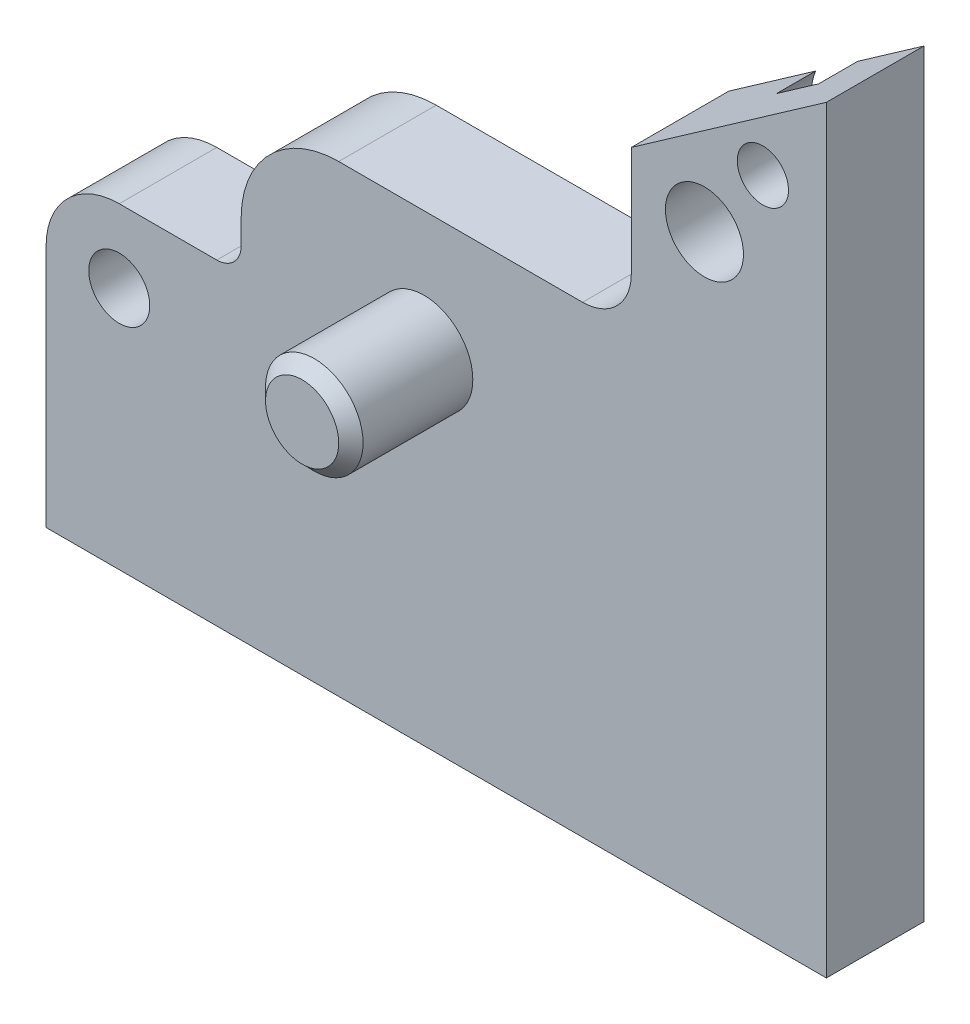
SolidWorks part; units mm, degrees
ref_plane "Front Plane" through (0, 0, 0) normal (0, 0, 1) x (1, 0, 0)
ref_plane "Top Plane" through (0, 0, 0) normal (0, 1, 0) x (1, 0, 0)
ref_plane "Right Plane" through (0, 0, 0) normal (1, 0, 0) x (0, 0, -1)
ref_plane "Plane1" through (0, 0, 4) normal (0, 0, 1) x (1, 0, 0)
sketch "Sketch1" plane through (0, 0, 4) normal (0, 0, 1) x (1, 0, 0)
  line L0 (32, 25.5) -> (0, 25.5)
  line L1 (0, 25.5) -> (0, 0)
  line L2 (0, 0) -> (32, 0)
  line L3 (32, 0) -> (32, 25.5)
extrude "Boss-Extrude1" add sketch "Sketch1" against normal blind 4
sketch "Sketch2" plane through (0, 0, 0) normal (0, 0, -1) x (-1, 0, 0)
  line L0 (-8, 25.5) -> (-8, 13)
  line L1 (-8, 13) -> (0, 13)
  line L2 (0, 13) -> (0, 25.5)
  line L3 (0, 25.5) -> (-8, 25.5)
extrude "Cut-Extrude1" cut sketch "Sketch2" against normal through all
sketch "Sketch3" plane through (0, 0, 0) normal (0, 0, -1) x (-1, 0, 0)
  line L0 (-24, 25.5) -> (-24, 19)
  line L1 (-24, 19) -> (-8, 19)
  line L2 (-8, 19) -> (-8, 25.5)
  line L3 (-8, 25.5) -> (-24, 25.5)
extrude "Cut-Extrude2" cut sketch "Sketch3" against normal through all
draft "Draft1" type of draft neutral plane draft angle 35 faces to draft 1 face at (28, 25.5, 2) neutral plane through (24, 25.5, 4) neutral plane normal (-1, 0, 0) parameters "D1"=35
ref_plane "Plane2" through (0, 5, 0) normal (0, 1, 0) x (1, 0, 0)
sketch "Sketch4" plane through (0, 5, 0) normal (0, 1, 0) x (1, 0, 0)
  line L0 (8, 5) -> (6, 5)
  line L1 (6, 5) -> (6, 0)
  line L2 (6, 0) -> (8, 0)
  line L3 (8, 0) -> (8, 5)
  line L4 (6, 5) -> (6, 0) construction
revolve "Revolve1" add sketch "Sketch4" angle 360 about L4
ref_plane "Plane3" through (0, 14, 0) normal (0, -1, 0) x (1, 0, 0)
sketch "Sketch5" plane through (0, 14, 0) normal (0, -1, 0) x (1, 0, 0)
  line L0 (17.5, 9) -> (15.5, 9)
  line L1 (15.5, 9) -> (15.5, 4)
  line L2 (15.5, 4) -> (17.5, 4)
  line L3 (17.5, 4) -> (17.5, 9)
  line L4 (15.5, 9) -> (15.5, 4) construction
revolve "Revolve2" add sketch "Sketch5" angle 360 about L4
hole_wizard "Ø2.5 (2.5) Diameter Hole1" positions "Sketch7" profile "Sketch6" hole size "Ø2.5" standard "ANSI Metric"
sketch "Sketch7" plane through (0, 0, 4) normal (0, 0, 1) x (1, 0, 0)
  point P0 (3, 10)
sketch "Sketch6" plane through (3, 10, 4) normal (1, 0, 0) x (0, -1, 0)
  line L0 (0, 0) -> (0, 9)
  line L1 (0, 9) -> (1.25, 9)
  line L2 (1.25, 9) -> (1.25, 0)
  line L5 (1.25, 0) -> (0, 0)
  line L11 (0, -6.35) -> (0, 107.95) construction
  dimension "Thru Hole Dia." = 2.5
  dimension "Thru Hole Depth" = 9
hole_wizard "Ø3.2 (3.2) Diameter Hole1" positions "Sketch9" profile "Sketch8" hole size "Ø3.2" standard "ANSI Metric"
sketch "Sketch9" plane through (0, 0, 0) normal (0, 0, -1) x (-1, 0, 0)
  point P0 (-27, 24)
sketch "Sketch8" plane through (27, 24, 0) normal (1, 0, 0) x (0, 1, 0)
  line L0 (0, 0) -> (0, 9)
  line L1 (0, 9) -> (1.6, 9)
  line L2 (1.6, 9) -> (1.6, 0)
  line L5 (1.6, 0) -> (0, 0)
  line L11 (0, -6.35) -> (0, 107.95) construction
  dimension "Thru Hole Dia." = 3.2
  dimension "Thru Hole Depth" = 9
hole_wizard "M4x0.7 Tapped Hole1" positions "Sketch11" profile "Sketch10" tap size "M4x0.7" standard "ANSI Metric"
sketch "Sketch11" plane through (0, 0, 0) normal (0, 0, -1) x (-1, 0, 0)
  point P0 (-29.396, 27.203)
sketch "Sketch10" plane through (29.396, 27.203, 0) normal (1, 0, 0) x (0, 1, 0)
  line L0 (0, 0) -> (0, 9)
  line L1 (0, 9) -> (1.05, 9)
  line L3 (1.05, 9) -> (1.05, 1.6)
  line L4 (1.05, 1.6) -> (2, 1.6)
  line L5 (2, 1.6) -> (2, 0)
  line L7 (2, 0) -> (0, 0)
  line L11 (0, -6.35) -> (0, 107.95) construction
  dimension "Thru Tap Drill Dia." = 2.1
  dimension "Thru Tap Drill Depth" = 9
  dimension "Thread Major Dia." = 4
  dimension "Thread Depth" = 1.6
hole_wizard "Ø2.5 (2.5) Diameter Hole2" positions "Sketch13" profile "Sketch12" hole size "Ø2.5" standard "ANSI Metric"
sketch "Sketch13" plane through (0, 0, 0) normal (0, -1, 0) x (-1, 0, 0)
  point P0 (-10, -2)
  point P1 (-19.5, -2)
  point P2 (-29, -2)
sketch "Sketch12" plane through (10, 0, 2) normal (1, 0, 0) x (0, 0, -1)
  line L0 (0, 0) -> (0, 8.2511)
  line L1 (0, 8.2511) -> (1.25, 7.5)
  line L2 (1.25, 7.5) -> (1.25, 0)
  line L5 (1.25, 0) -> (0, 0)
  line L10 (0, 8.2511) -> (-1.25, 7.5) construction
  line L11 (0, -6.35) -> (0, 107.95) construction
  dimension "Hole Dia." = 2.5
  dimension "Hole Depth" = 7.5
  dimension "Drill Angle" = 118
chamfer "Chamfer1" distance 0.5 angle 45 2 edges at (8, 5, -5) (13.5, 14, 9)
fillet "Fillet1" radius 1 1 edges at (8, 13, 2)
fillet "Fillet2" radius 2 1 edges at (24, 19, 2)
fillet "Fillet3" radius 3 1 edges at (0, 13, 2)
fillet "Fillet4" radius 4 1 edges at (8, 19, 2)
